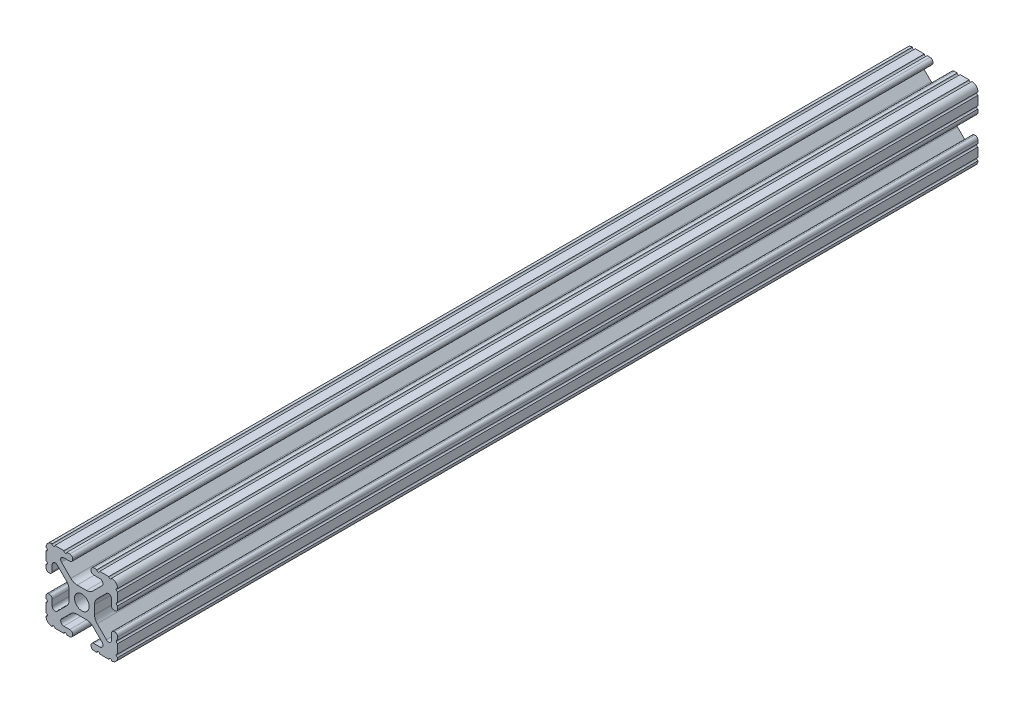
SolidWorks part; units mm, degrees
material "1060 Alloy"
ref_plane "Front Plane" through (0, 0, 0) normal (0, 0, 1) x (1, 0, 0)
ref_plane "Top Plane" through (0, 0, 0) normal (0, 1, 0) x (1, 0, 0)
ref_plane "Right Plane" through (0, 0, 0) normal (1, 0, 0) x (0, 0, -1)
sketch "Sketch1" plane through (0, 0, 0) normal (0, 0, 1) x (1, 0, 0)
  line L88 (-7.1797, -8.6452) -> (-3.9523, -5.4237)
  line L89 (-1.7093, -4.4958) -> (1.7093, -4.4958)
  line L90 (3.9523, -5.4237) -> (7.1797, -8.6452)
  line L91 (6.4164, -10.4902) -> (4.2875, -10.4902)
  line L92 (3.2385, -11.5392) -> (3.2385, -11.651)
  line L93 (4.2875, -12.7) -> (5.3171, -12.7)
  line L94 (6.3331, -12.7) -> (9.5504, -12.7)
  line L95 (12.7, -9.5504) -> (12.7, -6.3331)
  line L96 (12.7, -5.3171) -> (12.7, -4.2875)
  line L97 (11.651, -3.2385) -> (11.5392, -3.2385)
  line L98 (10.4902, -4.2875) -> (10.4902, -6.4021)
  line L99 (8.7371, -7.1294) -> (5.441, -3.8408)
  line L100 (4.5085, -1.5932) -> (4.5085, 1.5932)
  line L101 (5.441, 3.8408) -> (8.7371, 7.1294)
  line L102 (10.4902, 6.4021) -> (10.4902, 4.2875)
  line L103 (11.5392, 3.2385) -> (11.651, 3.2385)
  line L104 (12.7, 4.2875) -> (12.7, 5.3171)
  line L105 (12.7, 6.3331) -> (12.7, 9.5504)
  line L106 (9.5504, 12.7) -> (6.3331, 12.7)
  line L107 (5.3171, 12.7) -> (4.2875, 12.7)
  line L108 (3.2385, 11.651) -> (3.2385, 11.5392)
  line L109 (4.2875, 10.4902) -> (6.4768, 10.4902)
  line L110 (7.207, 8.7244) -> (3.8983, 5.4232)
  line L111 (1.6558, 4.4958) -> (-1.6558, 4.4958)
  line L112 (-3.8983, 5.4232) -> (-7.207, 8.7244)
  line L113 (-6.4768, 10.4902) -> (-4.2875, 10.4902)
  line L114 (-3.2385, 11.5392) -> (-3.2385, 11.651)
  line L115 (-4.2875, 12.7) -> (-5.3171, 12.7)
  line L116 (-6.3331, 12.7) -> (-9.5504, 12.7)
  line L117 (-12.7, 9.5504) -> (-12.7, 6.3331)
  line L118 (-12.7, 5.3171) -> (-12.7, 4.2875)
  line L119 (-11.651, 3.2385) -> (-11.5392, 3.2385)
  line L120 (-10.4902, 4.2875) -> (-10.4902, 6.4021)
  line L121 (-8.7371, 7.1294) -> (-5.441, 3.8408)
  line L122 (-4.5085, 1.5932) -> (-4.5085, -1.5932)
  line L123 (-5.441, -3.8408) -> (-8.7371, -7.1294)
  line L124 (-10.4902, -6.4021) -> (-10.4902, -4.2875)
  line L125 (-11.5392, -3.2385) -> (-11.651, -3.2385)
  line L126 (-12.7, -4.2875) -> (-12.7, -5.3171)
  line L127 (-12.7, -6.3331) -> (-12.7, -9.5504)
  line L128 (-9.5504, -12.7) -> (-6.3331, -12.7)
  line L129 (-5.3171, -12.7) -> (-4.2875, -12.7)
  line L130 (-3.2385, -11.651) -> (-3.2385, -11.5392)
  line L131 (-4.2875, -10.4902) -> (-6.4164, -10.4902)
  circle A1 centre (0, 0) radius 2.6035
  arc A104 (-7.1797, -8.6452) -> (-6.4164, -10.4902) centre (-6.4164, -9.4098) ccw
  arc A105 (-1.7093, -4.4958) -> (-3.9523, -5.4237) centre (-1.7093, -7.6708) ccw
  arc A106 (3.9523, -5.4237) -> (1.7093, -4.4958) centre (1.7093, -7.6708) ccw
  arc A107 (6.4164, -10.4902) -> (7.1797, -8.6452) centre (6.4164, -9.4098) ccw
  arc A108 (4.2875, -10.4902) -> (3.2385, -11.5392) centre (4.2875, -11.5392) ccw
  arc A109 (3.2385, -11.651) -> (4.2875, -12.7) centre (4.2875, -11.651) ccw
  arc A110 (6.3331, -12.7) -> (5.3171, -12.7) centre (5.8251, -12.7) ccw
  arc A111 (10.5664, -12.6998) -> (9.5504, -12.7) centre (10.0584, -12.7) ccw
  arc A112 (10.5664, -12.6998) -> (12.6998, -10.5664) centre (10.5918, -10.5918) ccw
  arc A113 (12.7, -9.5504) -> (12.6998, -10.5664) centre (12.7, -10.0584) ccw
  arc A114 (12.7, -5.3171) -> (12.7, -6.3331) centre (12.7, -5.8251) ccw
  arc A115 (12.7, -4.2875) -> (11.651, -3.2385) centre (11.651, -4.2875) ccw
  arc A116 (11.5392, -3.2385) -> (10.4902, -4.2875) centre (11.5392, -4.2875) ccw
  arc A117 (8.7371, -7.1294) -> (10.4902, -6.4021) centre (9.4628, -6.4021) ccw
  arc A118 (4.5085, -1.5932) -> (5.441, -3.8408) centre (7.6835, -1.5932) ccw
  arc A119 (5.441, 3.8408) -> (4.5085, 1.5932) centre (7.6835, 1.5932) ccw
  arc A120 (10.4902, 6.4021) -> (8.7371, 7.1294) centre (9.4628, 6.4021) ccw
  arc A121 (10.4902, 4.2875) -> (11.5392, 3.2385) centre (11.5392, 4.2875) ccw
  arc A122 (11.651, 3.2385) -> (12.7, 4.2875) centre (11.651, 4.2875) ccw
  arc A123 (12.7, 6.3331) -> (12.7, 5.3171) centre (12.7, 5.8251) ccw
  arc A124 (12.6998, 10.5664) -> (12.7, 9.5504) centre (12.7, 10.0584) ccw
  arc A125 (12.6998, 10.5664) -> (10.5664, 12.6998) centre (10.5918, 10.5918) ccw
  arc A126 (9.5504, 12.7) -> (10.5664, 12.6998) centre (10.0584, 12.7) ccw
  arc A127 (5.3171, 12.7) -> (6.3331, 12.7) centre (5.8251, 12.7) ccw
  arc A128 (4.2875, 12.7) -> (3.2385, 11.651) centre (4.2875, 11.651) ccw
  arc A129 (3.2385, 11.5392) -> (4.2875, 10.4902) centre (4.2875, 11.5392) ccw
  arc A130 (7.207, 8.7244) -> (6.4768, 10.4902) centre (6.4768, 9.4563) ccw
  arc A131 (1.6558, 4.4958) -> (3.8983, 5.4232) centre (1.6558, 7.6708) ccw
  arc A132 (-3.8983, 5.4232) -> (-1.6558, 4.4958) centre (-1.6558, 7.6708) ccw
  arc A133 (-6.4768, 10.4902) -> (-7.207, 8.7244) centre (-6.4768, 9.4563) ccw
  arc A134 (-4.2875, 10.4902) -> (-3.2385, 11.5392) centre (-4.2875, 11.5392) ccw
  arc A135 (-3.2385, 11.651) -> (-4.2875, 12.7) centre (-4.2875, 11.651) ccw
  arc A136 (-6.3331, 12.7) -> (-5.3171, 12.7) centre (-5.8251, 12.7) ccw
  arc A137 (-10.5664, 12.6998) -> (-9.5504, 12.7) centre (-10.0584, 12.7) ccw
  arc A138 (-10.5664, 12.6998) -> (-12.6998, 10.5664) centre (-10.5918, 10.5918) ccw
  arc A139 (-12.7, 9.5504) -> (-12.6998, 10.5664) centre (-12.7, 10.0584) ccw
  arc A140 (-12.7, 5.3171) -> (-12.7, 6.3331) centre (-12.7, 5.8251) ccw
  arc A141 (-12.7, 4.2875) -> (-11.651, 3.2385) centre (-11.651, 4.2875) ccw
  arc A142 (-11.5392, 3.2385) -> (-10.4902, 4.2875) centre (-11.5392, 4.2875) ccw
  arc A143 (-8.7371, 7.1294) -> (-10.4902, 6.4021) centre (-9.4628, 6.4021) ccw
  arc A144 (-4.5085, 1.5932) -> (-5.441, 3.8408) centre (-7.6835, 1.5932) ccw
  arc A145 (-5.441, -3.8408) -> (-4.5085, -1.5932) centre (-7.6835, -1.5932) ccw
  arc A146 (-10.4902, -6.4021) -> (-8.7371, -7.1294) centre (-9.4628, -6.4021) ccw
  arc A147 (-10.4902, -4.2875) -> (-11.5392, -3.2385) centre (-11.5392, -4.2875) ccw
  arc A148 (-11.651, -3.2385) -> (-12.7, -4.2875) centre (-11.651, -4.2875) ccw
  arc A149 (-12.7, -6.3331) -> (-12.7, -5.3171) centre (-12.7, -5.8251) ccw
  arc A150 (-12.6998, -10.5664) -> (-12.7, -9.5504) centre (-12.7, -10.0584) ccw
  arc A151 (-12.6998, -10.5664) -> (-10.5664, -12.6998) centre (-10.5918, -10.5918) ccw
  arc A152 (-9.5504, -12.7) -> (-10.5664, -12.6998) centre (-10.0584, -12.7) ccw
  arc A153 (-5.3171, -12.7) -> (-6.3331, -12.7) centre (-5.8251, -12.7) ccw
  arc A154 (-4.2875, -12.7) -> (-3.2385, -11.651) centre (-4.2875, -11.651) ccw
  arc A155 (-3.2385, -11.5392) -> (-4.2875, -10.4902) centre (-4.2875, -11.5392) ccw
extrude "Boss-Extrude1" add sketch "Sketch1" along normal blind 305
